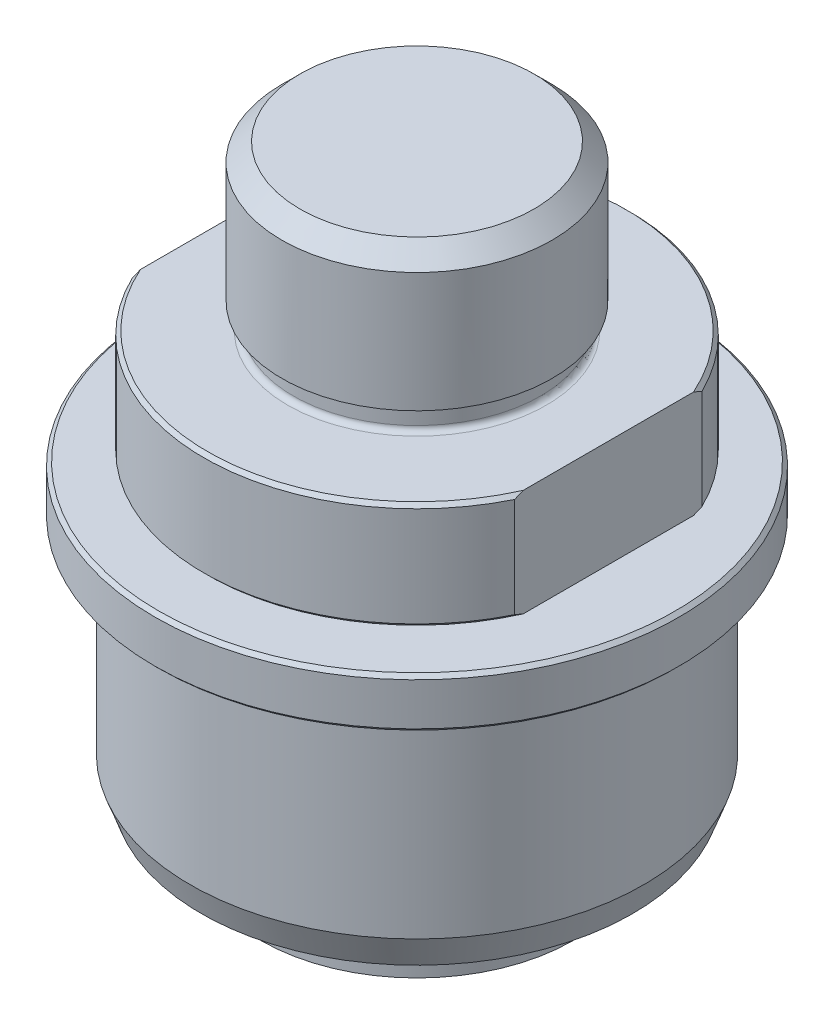
SolidWorks part; units mm, degrees
ref_plane "Front Plane" through (0, 0, 0) normal (0, 0, 1) x (1, 0, 0)
ref_plane "Top Plane" through (0, 0, 0) normal (0, 1, 0) x (1, 0, 0)
ref_plane "Right Plane" through (0, 0, 0) normal (1, 0, 0) x (0, 0, -1)
sketch "Sketch1" plane through (0, 0, 0) normal (0, 0, 1) x (1, 0, 0)
  line L0 (0, 23.114) -> (0, -36.6268)
  line L1 (0, 23.114) -> (19.05, 23.114)
  line L2 (19.05, 23.114) -> (19.05, 3.683)
  line L3 (18.2245, 0) -> (30.0482, 0)
  line L4 (30.0482, 0) -> (30.0482, -15.0876)
  line L5 (30.0482, -15.0876) -> (21.971, -15.0876)
  line L6 (21.971, -15.0876) -> (21.971, -58.293)
  line L7 (21.971, -63.5254) -> (16.6116, -63.5254)
  line L8 (0, 23.114) -> (0, 50.8132) construction
  line L9 (19.05, 3.683) -> (17.4625, 3.683)
  line L10 (17.4625, 3.683) -> (17.4625, 0.762)
  line L11 (15.0876, -62.0014) -> (15.0876, -47.0154)
  line L12 (15.0876, -47.0154) -> (4.699, -36.6268)
  line L13 (4.699, -36.6268) -> (0, -36.6268)
  line L14 (21.971, -60.833) -> (21.971, -63.5254)
  arc A0 (21.971, -58.293) -> (21.971, -60.833) centre (21.971, -59.563) ccw
  arc A1 (16.6116, -63.5254) -> (15.0876, -62.0014) centre (16.6116, -62.0014) cw
  arc A2 (18.2245, 0) -> (17.4625, 0.762) centre (18.2245, 0.762) cw
  dimension "D14" = 1.27
  dimension "D15" = 1.524
  dimension "D16" = 0.762
  dimension "D1" = 38.1
  dimension "D2" = 23.114
  dimension "D3" = 15.0876
  dimension "D4" = 63.5254
  dimension "D5" = 43.942
  dimension "D6" = 60.0964
  dimension "D7" = 3.683
  dimension "D8" = 34.925
  dimension "D9" = 30.1752
  dimension "D10" = 16.51
  dimension "D11" = 45
  dimension "D12" = 9.398
  dimension "D13" = 2.6924
revolve "Revolve1" add sketch "Sketch1" angle 360 about L8
chamfer "Chamfer1" distance 0.508 angle 45 2 edges at (0, -15.0876, -30.0482) (0, 0, -30.0482)
chamfer "Chamfer2" distance 2.54 angle 45 1 edges at (0, 23.114, -19.05)
sketch "Sketch4" plane through (0, 0, 0) normal (0, 1, 0) x (1, 0, 0)
  line L0 (-26.9875, 13.2125) -> (-26.9875, -13.2125)
  line L1 (26.9875, 13.2125) -> (26.9875, -13.2125)
  circle A0 centre (0, 0) radius 30.0482 construction
  arc A1 (26.9875, -13.2125) -> (26.9875, 13.2125) centre (0, 0) ccw
  arc A2 (-26.9875, 13.2125) -> (-26.9875, -13.2125) centre (0, 0) ccw
  dimension "D1" = 26.9875
  dimension "D2" = 26.9875
extrude "Cut-Extrude1" cut sketch "Sketch4" against normal through all
sketch "Sketch2" plane through (0, 0, 0) normal (0, 0, 1) x (1, 0, 0)
  line L0 (22.0218, -16.002) -> (22.0218, -50.6476)
  line L1 (25.0317, -56.007) -> (30.407, -56.007)
  line L2 (30.407, -56.007) -> (31.9786, -51.689)
  line L3 (31.9786, -51.689) -> (31.9786, -23.7744)
  line L4 (32.7406, -23.0124) -> (36.957, -23.0124)
  line L5 (36.957, -23.0124) -> (36.957, -16.002)
  line L6 (36.957, -16.002) -> (22.0218, -16.002)
  line L7 (0, 0) -> (0, 33.0062) construction
  line L8 (29.5402, 0) -> (-29.5402, 0) construction
  line L9 (21.971, -58.293) -> (21.971, -15.0876) construction
  line L11 (25.0317, -56.007) -> (25.0317, -51.6636)
  line L12 (24.0157, -50.6476) -> (22.0218, -50.6476)
  line L13 (21.971, -58.293) -> (-21.971, -58.293) construction
  line L14 (-21.971, -63.5254) -> (21.971, -63.5254) construction
  arc A0 (25.0317, -51.6636) -> (24.0157, -50.6476) centre (24.0157, -51.6636) ccw
  arc A1 (31.9786, -23.7744) -> (32.7406, -23.0124) centre (32.7406, -23.7744) cw
  dimension "D13" = 1.016
  dimension "D14" = 0.762
  dimension "D1" = 40.005
  dimension "D2" = 7.0104
  dimension "D3" = 63.9572
  dimension "D4" = 73.914
  dimension "D5" = 4.318
  dimension "D6" = 20
  dimension "D7" = 60.814
  dimension "D8" = 23.0124
  dimension "D9" = 0.0508
  dimension "D10" = 7.6454
  dimension "D11" = 7.5184
  dimension "D12" = 50.0634
revolve "Revolve2" add sketch "Sketch2" angle 360 about L7
chamfer "Chamfer3" distance 0.508 angle 45 2 edges at (0, -16.002, -36.957) (0, -23.0124, -36.957)
sketch "Sketch3" plane through (0, 0, 0) normal (0, 0, 1) x (1, 0, 0)
  line L1 (0, 0) -> (0, -31.4929) construction
  circle A0 centre (21.971, -59.563) radius 1.2192
  arc A2 (21.971, -58.293) -> (21.971, -60.833) centre (21.971, -59.563) ccw construction
  dimension "D1" = 0.0508
revolve "Revolve3" add sketch "Sketch3" angle 330 about L1
